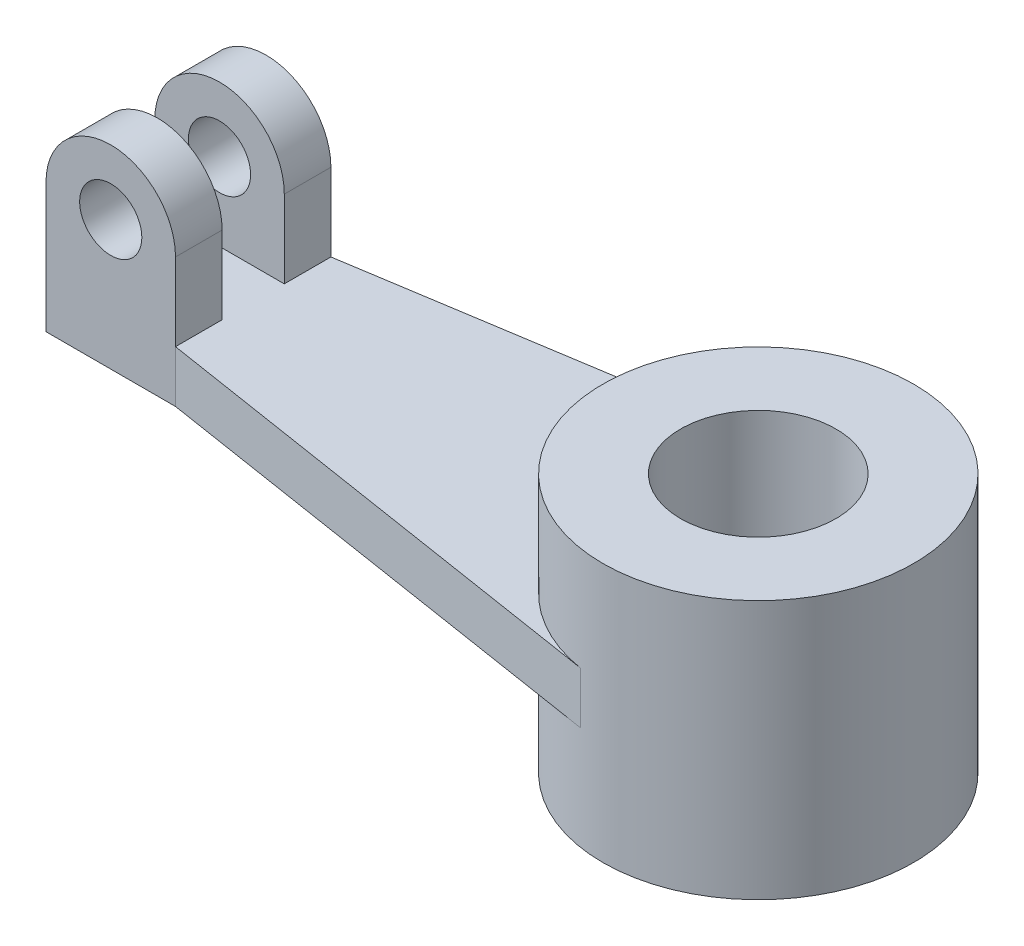
SolidWorks part; units mm, degrees
ref_plane "Front Plane" through (0, 0, 0) normal (0, 0, 1) x (1, 0, 0)
ref_plane "Top Plane" through (0, 0, 0) normal (0, 1, 0) x (1, 0, 0)
ref_plane "Right Plane" through (0, 0, 0) normal (1, 0, 0) x (0, 0, -1)
sketch "Sketch6" plane through (0, 0, 0) normal (0, 1, 0) x (1, 0, 0)
  line L0 (-122.5, 0) -> (120.8878, 0) construction
  line L1 (-110, 54.2331) -> (-110, -43.3643) construction
  line L2 (-122.5, 0) -> (-122.5, -15)
  line L3 (-122.5, -15) -> (-97.5, -15)
  line L4 (-97.5, -15) -> (-4.6717, -29.634)
  line L5 (-122.5, 0) -> (-15, 0)
  line L6 (15, 0) -> (30, 0)
  arc A0 (-30, 0) -> (30, 0) centre (0, 0) ccw
  arc A1 (-15, 0) -> (15, 0) centre (0, 0) ccw
  dimension "D1" = 60
  dimension "D2" = 30
  dimension "D3" = 110
  dimension "D4" = 122.5
  dimension "D5" = 25
  dimension "D6" = 15
extrude "Boss-Extrude2" add sketch "Sketch6" along normal mid plane 10 contours A0 L5 L2 L3 L4
sketch "Sketch7" plane through (0, 0, 0) normal (0, 1, 0) x (1, 0, 0)
  circle A0 centre (0, 0) radius 30
extrude "Boss-Extrude3" add sketch "Sketch7" along normal mid plane 50
sketch "Sketch8" plane through (0, 25, 0) normal (0, 1, 0) x (1, 0, 0)
  circle A0 centre (0, 0) radius 15
  dimension "D1" = 30
extrude "Cut-Extrude2" cut sketch "Sketch8" against normal blind 50
mirror "Mirror1" about plane through (0, 5, 0) normal (0, 0, -1) of "Boss-Extrude2"
sketch "Sketch9" plane through (0, 0, 15) normal (0, 0, 1) x (1, 0, 0)
  line L1 (-122.5, 5) -> (-97.5, 5)
  line L2 (-122.5, 5) -> (-122.5, 20)
  line L4 (-97.5, 5) -> (-97.5, 20)
  arc A0 (-97.5, 20) -> (-122.5, 20) centre (-110, 20) ccw
  dimension "D1" = 15
  dimension "D2" = 25
extrude "Boss-Extrude4" add sketch "Sketch9" against normal blind 9
sketch "Sketch10" plane through (0, 0, 15) normal (0, 0, 1) x (1, 0, 0)
  circle A0 centre (-110, 20) radius 6
  dimension "D1" = 12
extrude "Cut-Extrude3" cut sketch "Sketch10" against normal blind 9
sketch "Sketch11" plane through (0, 0, -15) normal (0, 0, -1) x (-1, 0, 0)
  line L0 (122.5, 5) -> (97.5, 5) construction
  line L1 (122.5, 5) -> (97.5, 5)
  line L2 (122.5, 5) -> (122.5, 20)
  line L4 (97.5, 5) -> (97.5, 20)
  line L5 (122.5, 5) -> (122.5, -5) construction
  arc A0 (122.5, 20) -> (97.5, 20) centre (110, 20) ccw
  dimension "D1" = 15
  dimension "D2" = 25
extrude "Boss-Extrude5" add sketch "Sketch11" against normal blind 9
sketch "Sketch12" plane through (0, 0, -15) normal (0, 0, -1) x (-1, 0, 0)
  circle A0 centre (110, 20) radius 6
  dimension "D1" = 12
extrude "Cut-Extrude4" cut sketch "Sketch12" against normal blind 9
